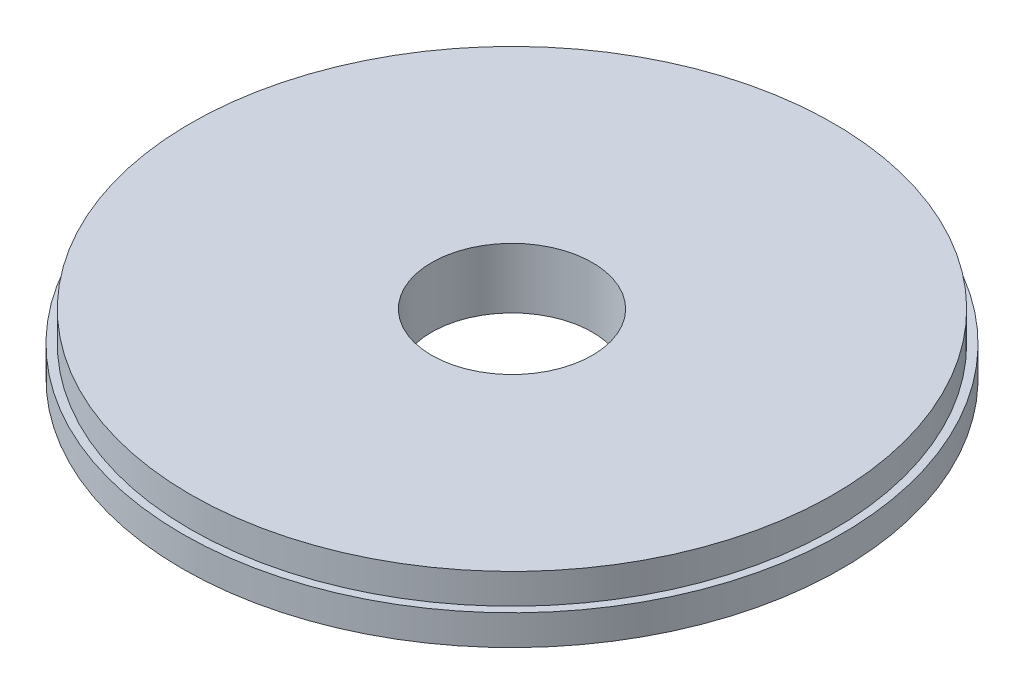
SolidWorks part; units mm, degrees
ref_plane "Front Plane" through (0, 0, 0) normal (0, 0, 1) x (1, 0, 0)
ref_plane "Top Plane" through (0, 0, 0) normal (0, 1, 0) x (1, 0, 0)
ref_plane "Right Plane" through (0, 0, 0) normal (1, 0, 0) x (0, 0, -1)
sketch "Sketch1" plane through (0, 0, 0) normal (0, 1, 0) x (1, 0, 0)
  circle A0 centre (0, 0) radius 101.6
  circle A1 centre (0, 0) radius 25.4
  dimension "D1" = 203.2
  dimension "D2" = 50.8
extrude "Boss-Extrude1" add sketch "Sketch1" along normal mid plane 19.05
sketch "Sketch2" plane through (0, -9.525, 0) normal (0, 1, 0) x (1, 0, 0)
  circle A0 centre (0, 0) radius 101.6 construction
  circle A1 centre (0, 0) radius 101.6
  circle A2 centre (0, 0) radius 104.14
  dimension "D1" = 2.54
extrude "Boss-Extrude2" add sketch "Sketch2" against normal up to surface (9.525 mm away)
